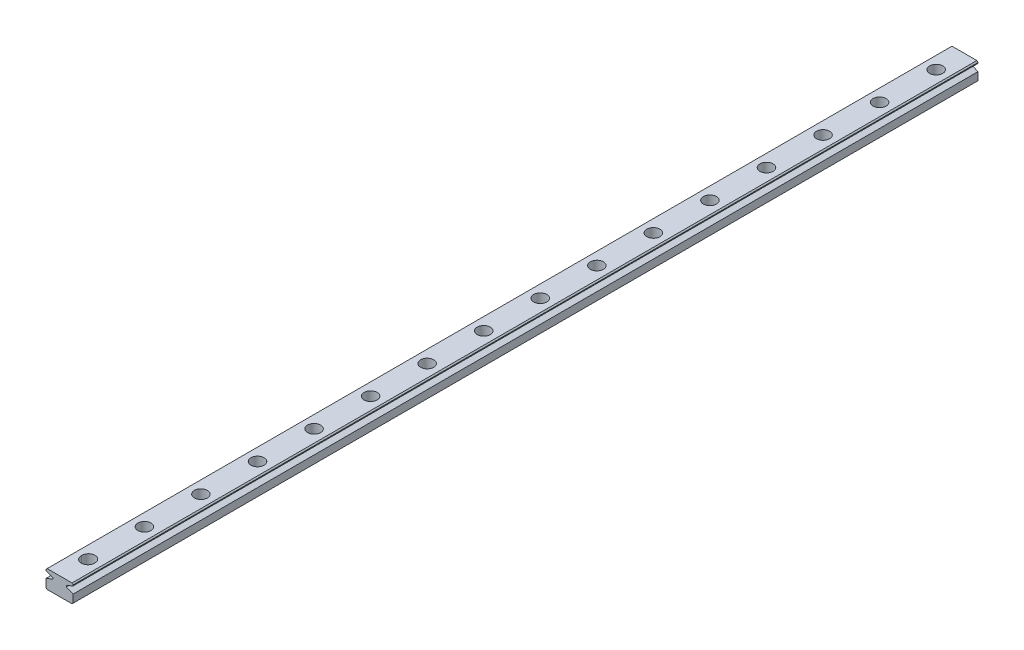
SolidWorks part; units mm, degrees
ref_plane "前视基准面" through (0, 0, 0) normal (0, 0, 1) x (1, 0, 0)
ref_plane "上视基准面" through (0, 0, 0) normal (0, 1, 0) x (1, 0, 0)
ref_plane "右视基准面" through (0, 0, 0) normal (1, 0, 0) x (0, 0, -1)
sketch "草图1" plane through (0, 0, 0) normal (0, 0, 1) x (1, 0, 0)
  line L0 (5.6176, 4.2219) -> (16.6176, 4.2219)
  line L1 (5.1176, 4.7219) -> (5.1176, 8.2219)
  line L2 (5.6176, 12.2219) -> (16.6176, 12.2219)
  line L3 (17.1176, 11.7219) -> (17.1176, 11.3434)
  line L4 (-0.6651, 7.7219) -> (23.2604, 7.7219) construction
  line L5 (8.1176, 15.7502) -> (8.1176, 0) construction
  line L6 (14.1176, 15.7502) -> (14.1176, 0) construction
  line L7 (17.1176, 8.2219) -> (14.1176, 9.4454)
  line L8 (8.1176, 9.4454) -> (5.1176, 8.2219)
  line L9 (8.1176, 9.9878) -> (8.1176, 9.4454)
  line L10 (14.1176, 9.9878) -> (17.1176, 11.3434)
  line L11 (14.1176, 9.9878) -> (14.1176, 9.4454)
  line L12 (8.1176, 9.9878) -> (5.1176, 11.2113)
  line L13 (5.1176, 11.2113) -> (5.1176, 11.7219)
  line L14 (17.1176, 8.2219) -> (17.1176, 4.7219)
  line L15 (5.1176, 11.7219) -> (5.6176, 12.2219)
  line L16 (16.6176, 12.2219) -> (17.1176, 11.7219)
  line L17 (5.6176, 4.2219) -> (5.1176, 4.7219)
  line L18 (17.1176, 4.7219) -> (16.6176, 4.2219)
  point P0 (5.1176, 4.2219)
  point P1 (17.1176, 4.2219)
  point P2 (5.1176, 12.2219)
  point P3 (17.1176, 12.2219)
  dimension "D1" = 12
  dimension "D2" = 8
  dimension "D3" = 4.5
  dimension "D4" = 3
  dimension "D5" = 3
extrude "凸台-拉伸1" add sketch "草图1" along normal blind 400
sketch "草图8" plane through (0, 12.2219, 0) normal (0, 1, 0) x (1, 0, 0)
  line L0 (11.1176, -400) -> (11.1176, 0)
  line L1 (16.6176, -400) -> (5.6176, -400) construction
  line L2 (16.6176, 0) -> (5.6176, 0) construction
sketch "草图11" plane through (0, 12.2219, 0) normal (0, 1, 0) x (1, 0, 0)
  line L0 (11.1176, -400) -> (11.1176, 0) construction
  line L1 (11.1176, -200) -> (-23.6842, -200)
  line L2 (-6.6027, -187.5) -> (21.1979, -187.5) construction
  line L3 (-6.6027, -137.5) -> (26.1227, -137.5) construction
  line L4 (-5.431, -162.5) -> (24.3933, -162.5) construction
  line L5 (-6.6027, -112.5) -> (26.1227, -112.5) construction
  line L6 (-7.9103, -87.5) -> (27.1719, -87.5) construction
  line L7 (-6.6027, -62.5) -> (27.1719, -62.5) construction
  line L8 (-7.9103, -37.5) -> (27.1719, -37.5) construction
  line L9 (-7.9103, -12.5) -> (27.1719, -12.5) construction
  line L10 (-6.6027, -212.5) -> (21.1979, -212.5) construction
  line L11 (-7.9103, -387.5) -> (27.1719, -387.5) construction
  line L12 (-7.9103, -362.5) -> (27.1719, -362.5) construction
  line L13 (-6.6027, -337.5) -> (27.1719, -337.5) construction
  line L14 (-7.9103, -312.5) -> (27.1719, -312.5) construction
  line L15 (-6.6027, -287.5) -> (26.1227, -287.5) construction
  line L16 (-6.6027, -262.5) -> (26.1227, -262.5) construction
  line L17 (-5.431, -237.5) -> (24.3933, -237.5) construction
  dimension "D1" = 25
  dimension "D2" = 12.5
  dimension "D3" = 25
  dimension "D4" = 25
  dimension "D5" = 25
  dimension "D6" = 25
  dimension "D7" = 25
  dimension "D8" = 25
hole_wizard "孔4" positions "3D草图4" profile "草图12" legacy end condition through all
sketch3d "3D草图4"
  line L0 (11.1176, 12.2219, 400) -> (11.1176, 12.2219, 0) construction
  line L1 (-7.9103, 12.2219, 387.5) -> (27.1719, 12.2219, 387.5) construction
  line L2 (-7.9103, 12.2219, 362.5) -> (27.1719, 12.2219, 362.5) construction
  line L3 (-7.9103, 12.2219, 312.5) -> (27.1719, 12.2219, 312.5) construction
  line L4 (-6.6027, 12.2219, 287.5) -> (26.1227, 12.2219, 287.5) construction
  line L5 (-5.431, 12.2219, 237.5) -> (24.3933, 12.2219, 237.5) construction
  line L6 (-6.6027, 12.2219, 212.5) -> (21.1979, 12.2219, 212.5) construction
  line L7 (-6.6027, 12.2219, 187.5) -> (21.1979, 12.2219, 187.5) construction
  line L8 (-5.431, 12.2219, 162.5) -> (24.3933, 12.2219, 162.5) construction
  line L9 (-6.6027, 12.2219, 137.5) -> (26.1227, 12.2219, 137.5) construction
  line L10 (-6.6027, 12.2219, 112.5) -> (26.1227, 12.2219, 112.5) construction
  line L11 (-7.9103, 12.2219, 87.5) -> (27.1719, 12.2219, 87.5) construction
  line L12 (-6.6027, 12.2219, 62.5) -> (27.1719, 12.2219, 62.5) construction
  line L13 (-7.9103, 12.2219, 37.5) -> (27.1719, 12.2219, 37.5) construction
  line L14 (-7.9103, 12.2219, 12.5) -> (27.1719, 12.2219, 12.5) construction
  point P0 (11.1176, 12.2219, 387.5)
  point P6 (11.1176, 12.2219, 362.5)
  point P10 (11.1176, 12.2219, 337.5245)
  point P12 (11.1176, 12.2219, 312.5)
  point P16 (11.1176, 12.2219, 287.5)
  point P20 (11.1176, 12.2219, 262.4995)
  point P22 (11.1176, 12.2219, 237.5)
  point P26 (11.1176, 12.2219, 212.5)
  point P30 (11.1176, 12.2219, 187.5)
  point P34 (11.1176, 12.2219, 162.5)
  point P38 (11.1176, 12.2219, 137.5)
  point P42 (11.1176, 12.2219, 112.5)
  point P46 (11.1176, 12.2219, 87.5)
  point P50 (11.1176, 12.2219, 62.5)
  point P54 (11.1176, 12.2219, 37.5)
  point P58 (11.1176, 12.2219, 12.5)
sketch "草图12" plane through (11.1176, 12.2219, 387.5) normal (1, 0, 0) x (0, 0, 1)
  line L0 (0, 0) -> (0, 8)
  line L1 (0, 8) -> (1.75, 8)
  line L2 (1.75, 8) -> (1.75, 4.5)
  line L3 (1.75, 4.5) -> (2.9, 4.5)
  line L4 (2.9, 4.5) -> (2.9, 0)
  line L5 (2.9, 0) -> (0, 0)
  line L6 (0, 110) -> (0, -10) construction
  dimension "直径" = 3.5
  dimension "深度" = 8
  dimension "柱坑直径" = 5.8
  dimension "柱坑深度" = 4.5
hole_wizard "孔3" positions "3D草图3" profile "草图9" legacy
sketch3d "3D草图3"
  line L0 (11.1176, 12.2219, 400) -> (11.1176, 12.2219, 0) construction
  point P0 (11.1176, 12.2219, 387.2239)
sketch "草图9" plane through (11.1176, 12.2219, 387.2239) normal (1, 0, 0) x (0, 0, 1)
  line L0 (0, 0) -> (0, 7.9169)
  line L1 (0, 7.9169) -> (1.75, 7.9169)
  line L2 (1.75, 7.9169) -> (1.75, 4.5)
  line L3 (1.75, 4.5) -> (2.9, 4.5)
  line L4 (2.9, 4.5) -> (2.9, 0)
  line L5 (2.9, 0) -> (0, 0)
  line L6 (0, 110) -> (0, -10) construction
  dimension "直径" = 3.5
  dimension "深度" = 8
  dimension "柱坑直径" = 5.8
  dimension "柱坑深度" = 4.5
